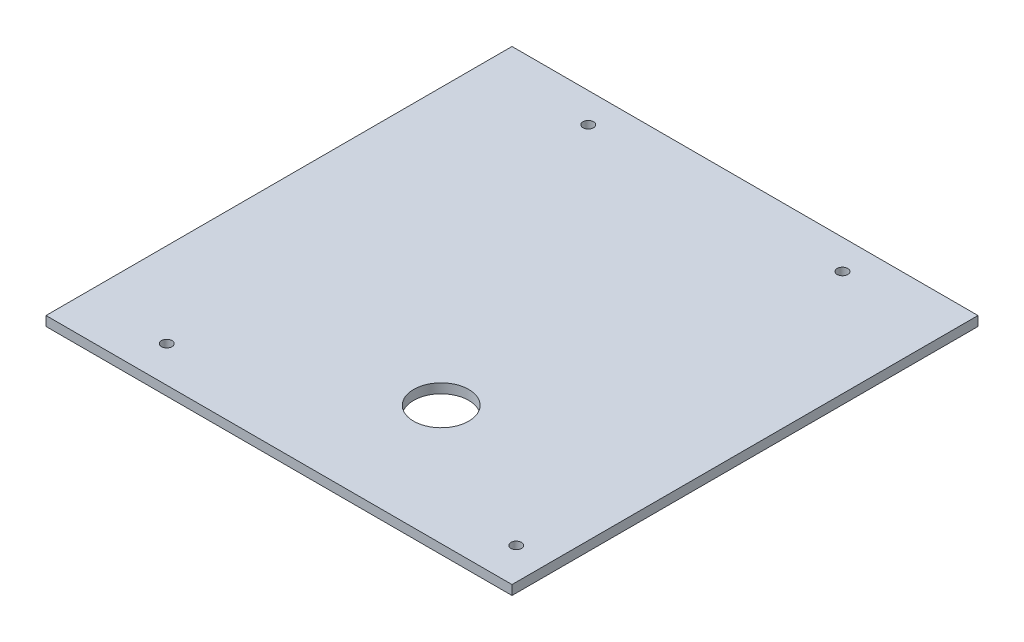
SolidWorks part; units mm, degrees
ref_plane "Front" through (0, 0, 0) normal (0, 0, 1) x (1, 0, 0)
ref_plane "Top" through (0, 0, 0) normal (0, 1, 0) x (1, 0, 0)
ref_plane "Right" through (0, 0, 0) normal (1, 0, 0) x (0, 0, -1)
sketch "Sketch1" plane through (0, 0, 0) normal (0, 1, 0) x (1, 0, 0)
  line L1 (-110, -110) -> (110, -110)
  line L2 (-110, -110) -> (-110, 110)
  line L3 (-110, 110) -> (110, 110)
  line L4 (110, -110) -> (110, 110)
  line L5 (-110, -110) -> (110, 110) construction
  line L6 (-110, 110) -> (110, -110) construction
  point P0 (0, 0)
  dimension "D1" = 220
  dimension "D2" = 220
extrude "Boss-Extrude1" add sketch "Sketch1" along normal blind 4.5
sketch "Sketch2" plane through (0, 4.5, 0) normal (0, 1, 0) x (1, 0, 0)
  line L5 (-110, -110) -> (110, -110) construction
  line L6 (110, -110) -> (110, 110) construction
  circle A0 centre (20, -53.4315) radius 13
  point P15 (0, -110)
  dimension "D4" = 26
  dimension "D5" = 90
  dimension "D9" = 60
extrude "Cut-Extrude1" cut sketch "Sketch2" against normal up to next
sketch "Sketch3" plane through (0, 4.5, 0) normal (0, 1, 0) x (1, 0, 0)
  line L0 (110, -110) -> (110, 110) construction
  line L1 (-110, -110) -> (110, -110) construction
  circle A0 centre (95, -93) radius 2.5
  circle A1 centre (-70, -93) radius 2.5
  point P4 (0, 0)
  dimension "D1" = 5
  dimension "D2" = 5
  dimension "D3" = 165
  dimension "D4" = 15
  dimension "D5" = 17
  dimension "D6" = 17
extrude "Cut-Extrude2" cut sketch "Sketch3" against normal up to next
sketch "Sketch4" plane through (0, 0, 0) normal (0, -1, 0) x (-1, 0, 0)
  circle A0 centre (-60, 96) radius 2.5
  circle A1 centre (60, 96) radius 2.5
extrude "Cut-Extrude3" cut sketch "Sketch4" against normal up to next
